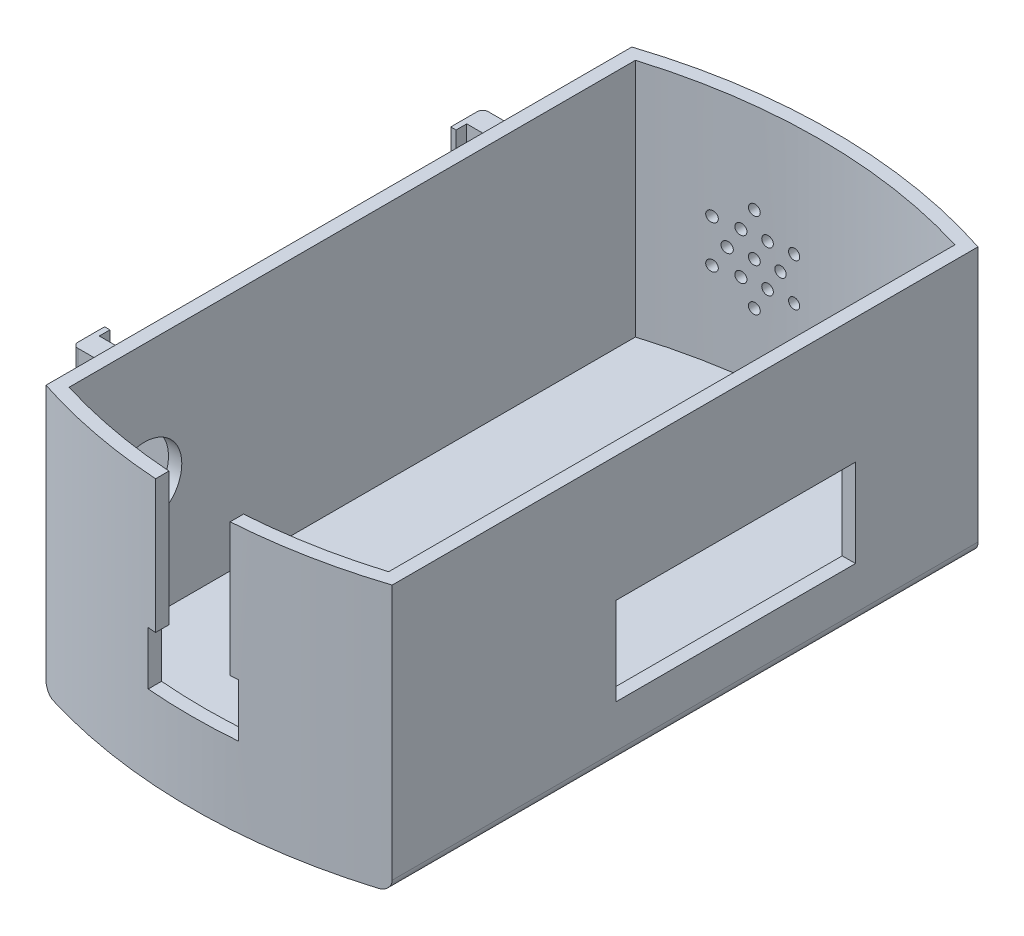
SolidWorks part; units mm, degrees
ref_plane "Front Plane" through (0, 0, 0) normal (0, 0, 1) x (1, 0, 0)
ref_plane "Top Plane" through (0, 0, 0) normal (0, 1, 0) x (1, 0, 0)
ref_plane "Right Plane" through (0, 0, 0) normal (1, 0, 0) x (0, 0, -1)
sketch "Sketch1" plane through (0, 0, 0) normal (0, 1, 0) x (1, 0, 0)
  line L0 (0, 0) -> (0, 103.3833) construction
  line L2 (-32.5, 55) -> (-32.5, -55)
  line L4 (32.5, 55) -> (32.5, -55)
  line L5 (-32.5, 55) -> (32.5, -55) construction
  line L6 (-32.5, -55) -> (32.5, 55) construction
  line L7 (0, 0) -> (47.7539, 0) construction
  arc A0 (32.5, 55) -> (-32.5, 55) centre (0, -44.8436) ccw
  arc A1 (32.5, -55) -> (-32.5, -55) centre (0, 44.8436) cw
  point P0 (0, 0)
  dimension "D3" = 210
  dimension "D1" = 65
  dimension "D2" = 110
extrude "Boss-Extrude1" add sketch "Sketch1" along normal blind 50
shell "Shell2" thickness 2.5
sketch "Sketch3" plane through (32.5, 0, 0) normal (1, 0, 0) x (0, 0, -1)
  line L1 (-13, 26.5) -> (32, 26.5)
  line L2 (-13, 26.5) -> (-13, 10)
  line L3 (-13, 10) -> (32, 10)
  line L4 (32, 26.5) -> (32, 10)
  line L5 (-55, 0) -> (55, 0) construction
  line L6 (-55, 50) -> (-55, 0) construction
  dimension "D1" = 45
  dimension "D2" = 16.5
  dimension "D3" = 42
  dimension "D4" = 10
sketch "Sketch11" plane through (-32.5, 0, 0) normal (-1, 0, 0) x (0, 0, 1)
  line L1 (-55, 50) -> (55, 50) construction
  line L2 (55, 50) -> (55, 0) construction
  circle A0 centre (39, 27) radius 7
  dimension "D1" = 14
  dimension "D2" = 16
  dimension "D3" = 23
extrude "Cut-Extrude7" cut sketch "Sketch11" against normal blind 20
fillet "Fillet1" radius 2 2 edges at (32.5, 0, 0) (-32.5, 0, 0)
sketch "Sketch16" plane through (-32.5, 0, 0) normal (-1, 0, 0) x (0, 0, 1)
  line L0 (-41, 2) -> (-41, 5)
  line L1 (-55, 2) -> (55, 2) construction
  line L2 (-41, 5) -> (14, 5)
  line L3 (14, 5) -> (14, 2)
  line L4 (14, 2) -> (-41, 2)
  line L5 (27, 31) -> (27, 6)
  line L6 (27, 6) -> (23, 6)
  line L7 (23, 6) -> (23, 31)
  line L8 (23, 31) -> (27, 31)
  line L9 (-50, 6) -> (-50, 31)
  line L10 (-50, 31) -> (-46, 31)
  line L11 (-46, 31) -> (-46, 6)
  line L12 (-46, 6) -> (-50, 6)
  line L14 (-55, 50) -> (-55, 2) construction
  dimension "D1" = 55
  dimension "D2" = 3
  dimension "D3" = 5
  dimension "D4" = 4
  dimension "D5" = 25
  dimension "D6" = 25
  dimension "D7" = 4
  dimension "D8" = 69
  dimension "D9" = 5
  dimension "D10" = 1
  dimension "D11" = 1
extrude "Boss-Extrude7" add sketch "Sketch16" along normal blind 22
sketch "Sketch17" plane through (0, 0, -46) normal (0, 0, 1) x (1, 0, 0)
  line L0 (-54.5, 31) -> (-54.5, 6)
  line L1 (-54.5, 6) -> (-55.5, 6)
  line L2 (-55.5, 6) -> (-55.5, 31)
  line L3 (-55.5, 31) -> (-54.5, 31)
  dimension "D1" = 1
extrude "Boss-Extrude8" add sketch "Sketch17" along normal blind 6 from surface at -4 starting at face at (-43.5, 18.5, -50)
sketch "Sketch18" plane through (0, 0, 27) normal (0, 0, 1) x (1, 0, 0)
  line L0 (-54.5, 31) -> (-54.5, 6)
  line L1 (-54.5, 6) -> (-55.5, 6)
  line L2 (-55.5, 6) -> (-55.5, 31)
  line L3 (-55.5, 31) -> (-54.5, 31)
extrude "Boss-Extrude9" add sketch "Sketch18" against normal blind 6
fillet "Fillet3" radius 1 2 edges at (-55.5, 18.5, 27) (-55.5, 18.5, -50)
extrude "Cut-Extrude8" cut sketch "Sketch3" against normal blind 10
sketch "Sketch20" plane through (0, 0, 0) normal (0, 0, 1) x (1, 0, 0)
  line L0 (32.5, 50) -> (32.5, 2) construction
  line L1 (-30.5, 0) -> (30.5, 0) construction
  circle A0 centre (20.5, 25) radius 2.55
  circle A1 centre (12.5, 25) radius 2.55
  dimension "D1" = 5.1
  dimension "D4" = 5.1
  dimension "D2" = 12
  dimension "D3" = 25
  dimension "D5" = 8
extrude "Cut-Extrude9" cut sketch "Sketch20" against normal blind 100
sketch "Sketch21" plane through (0, 0, 0) normal (0, 0, 1) x (1, 0, 0)
  line L0 (-30.5, 0) -> (30.5, 0) construction
  line L1 (-32.5, 50) -> (-32.5, 2) construction
  circle A0 centre (-11.5, 25) radius 1
  circle A1 centre (-7, 25) radius 1
  circle A2 centre (-9.25, 21.1029) radius 1
  circle A3 centre (-13.75, 21.1029) radius 1
  circle A4 centre (-16, 25) radius 1
  circle A5 centre (-13.75, 28.8971) radius 1
  circle A6 centre (-9.25, 28.8971) radius 1
  circle A7 centre (-11.5, 33) radius 1
  circle A8 centre (-4.5718, 29) radius 1
  circle A9 centre (-4.5718, 21) radius 1
  circle A10 centre (-11.5, 17) radius 1
  circle A11 centre (-18.4282, 21) radius 1
  circle A12 centre (-18.4282, 29) radius 1
  point P21 (-11.5, 25)
  point P33 (-11.5, 25)
  dimension "D3" = 2
  dimension "D5" = 2
  dimension "D7" = 2
  dimension "D1" = 25
  dimension "D2" = 21
  dimension "D4" = 4.5
  dimension "D8" = 8
  dimension "D6" = 6
  dimension "D9" = 6
extrude "Cut-Extrude10" cut sketch "Sketch21" against normal blind 100
sketch "Sketch22" plane through (0, 0, 0) normal (0, 0, 1) x (1, 0, 0)
  line L0 (-7, 25) -> (-7, 50)
  line L1 (-8.5, 25) -> (-7, 25)
  line L2 (-8.5, 25) -> (-8.5, 15)
  line L3 (-8.5, 15) -> (8.5, 15)
  line L4 (8.5, 25) -> (8.5, 15)
  line L5 (-8.5, 25) -> (8.5, 15) construction
  line L6 (-8.5, 15) -> (8.5, 25) construction
  line L7 (32.5, 50) -> (-32.5, 50) construction
  line L8 (-7, 50) -> (7, 50)
  line L9 (7, 50) -> (7, 25)
  line L10 (0, 25) -> (0, 53.7232) construction
  line L11 (7, 25) -> (8.5, 25)
  point P0 (0, 20)
  dimension "D1" = 17
  dimension "D2" = 10
  dimension "D3" = 20
  dimension "D4" = 14
extrude "Cut-Extrude11" cut sketch "Sketch22" along normal blind 100
